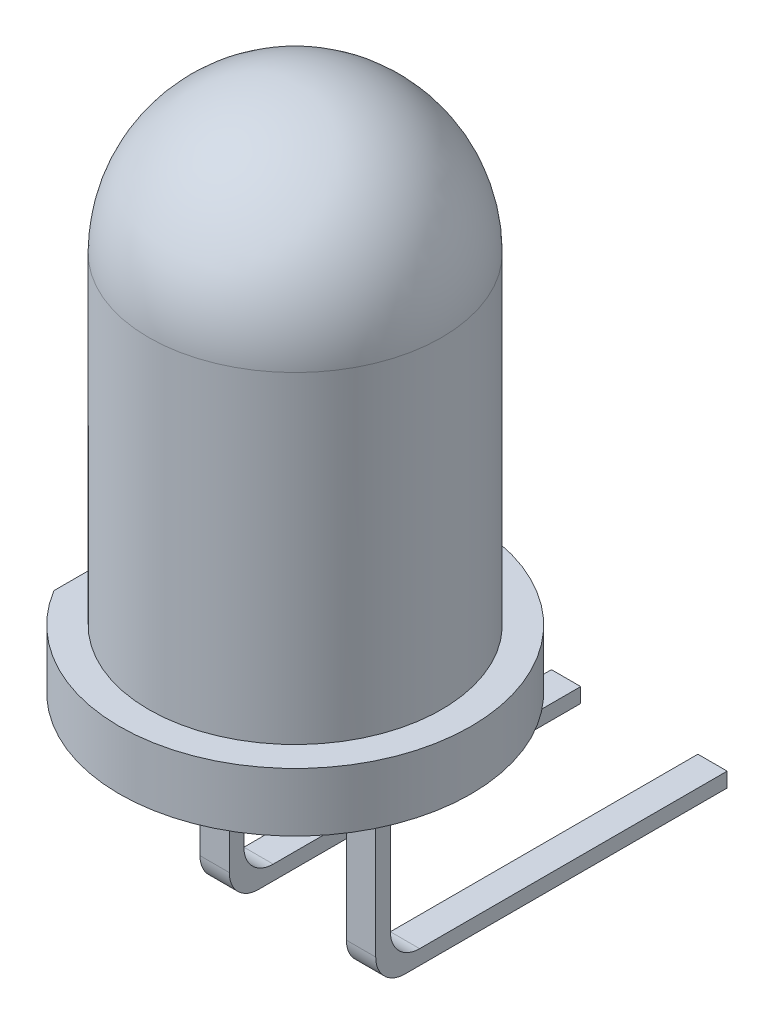
SolidWorks part; units mm, degrees
ref_plane "Front Plane" through (0, 0, 0) normal (0, 0, 1) x (1, 0, 0)
ref_plane "Top Plane" through (0, 0, 0) normal (0, 1, 0) x (1, 0, 0)
ref_plane "Right Plane" through (0, 0, 0) normal (1, 0, 0) x (0, 0, -1)
sketch "Sketch1" plane through (0, 0, 0) normal (0, 0, 1) x (1, 0, 0)
  line L0 (0, 40.4813) -> (0, -45.6712) construction
  line L3 (0, 2.5) -> (0, -5.5)
  line L5 (2.5, 0) -> (2.5, -5.5)
  line L6 (2.5, -5.5) -> (3, -5.5)
  line L7 (0, -5.5) -> (0, -6.5)
  line L8 (0, -6.5) -> (3, -6.5)
  line L9 (3, -5.5) -> (3, -6.5)
  arc A0 (2.5, 0) -> (0, 2.5) centre (0, 0) ccw
  dimension "D1" = 5
  dimension "D2" = 9
  dimension "D3" = 3
  dimension "D4" = 1
revolve "Revolve1" add sketch "Sketch1" angle 360 about L0
sketch "Sketch2" plane through (0, -6.5, 0) normal (0, -1, 0) x (1, 0, 0)
  line L0 (0, 0.7494) -> (0, -0.7682) construction
  line L1 (1, 0.125) -> (1.5, 0.125)
  line L2 (1, 0.125) -> (1, -0.125)
  line L3 (1, -0.125) -> (1.5, -0.125)
  line L4 (1.5, 0.125) -> (1.5, -0.125)
  line L5 (-1, 0.125) -> (-1, -0.125)
  line L6 (-1.5, 0.125) -> (-1.5, -0.125)
  line L7 (-1, -0.125) -> (-1.5, -0.125)
  line L8 (-1, 0.125) -> (-1.5, 0.125)
  line L9 (3.3, 0) -> (-3.3, 0) construction
  point P5 (1, 0)
  dimension "D1" = 0.25
  dimension "D2" = 0.5
  dimension "D3" = 1
extrude "Extrude1" add sketch "Sketch2" along normal blind 30
sketch "Sketch3" plane through (0, 0, 0) normal (0, 0, 1) x (1, 0, 0)
  line L0 (-1.5, -36.5) -> (-1.5, -6.5) construction
  line L1 (-1.5, -26.5) -> (-1, -26.5)
  line L2 (-1.5, -26.5) -> (-1.5, -36.5)
  line L3 (-1.5, -36.5) -> (-1, -36.5)
  line L4 (-1, -26.5) -> (-1, -36.5)
  line L5 (-1, -36.5) -> (-1, -6.5) construction
  dimension "D1" = 10
extrude "Extrude3" cut sketch "Sketch3" against normal blind 2 and the other way blind 2
sketch "Sketch4" plane through (0, -6.5, 0) normal (0, -1, 0) x (1, 0, 0)
  line L1 (-2.5675, 1.75) -> (-3.0675, 1.75)
  line L2 (-2.5675, 1.75) -> (-2.5675, -1.75)
  line L3 (-2.5675, -1.75) -> (-3.0675, -1.75)
  line L4 (-3.0675, 1.75) -> (-3.0675, -1.75)
  point P4 (-2.5675, 0)
  dimension "D1" = 3.5
  dimension "D2" = 0.5
extrude "Extrude4" cut sketch "Sketch4" against normal blind 2
sketch "Sketch5" plane through (-1.5, 0, 0) normal (-1, 0, 0) x (0, 0, 1)
  line L0 (0.125, -10.0975) -> (-5.875, -10.0975)
  line L1 (0.125, -26.5) -> (0.125, -6.5) construction
  line L2 (-5.875, -10.0975) -> (-5.875, -9.8475)
  line L3 (-5.875, -9.8475) -> (-0.125, -9.8475)
  line L4 (-0.125, -26.5) -> (-0.125, -6.5) construction
  line L5 (-0.125, -9.8475) -> (0.125, -10.0975)
  dimension "D1" = 0.25
  dimension "D2" = 6
extrude "Boss-Extrude1" add sketch "Sketch5" against normal up to surface (3 mm away) up to face at (1.5, -21.5, 0)
sketch "Sketch6" plane through (0, 0, 0.125) normal (0, 0, 1) x (1, 0, 0)
  line L0 (-1, -8.9519) -> (1, -8.9519)
  line L1 (-1, -10.0975) -> (-1, -6.5) construction
  line L2 (1, -10.0975) -> (1, -6.5) construction
  line L3 (1, -8.9519) -> (1, -10.0975)
  line L4 (1, -10.0975) -> (1.5, -10.0975)
  line L5 (1.5, -36.5) -> (1.5, -6.5) construction
  line L6 (1.5, -10.0975) -> (1.5, -37.4522)
  line L7 (1.5, -37.4522) -> (-1.5, -37.4522)
  line L8 (-1.5, -37.4522) -> (-1.5, -10.0975)
  line L9 (-1.5, -26.5) -> (-1.5, -6.5) construction
  line L10 (-1.5, -10.0975) -> (-1, -10.0975)
  line L11 (-1, -10.0975) -> (-1, -8.9519)
extrude "Cut-Extrude1" cut sketch "Sketch6" against normal blind 10
fillet "Fillet1" radius 0.5 4 edges at (1.25, -9.8475, -0.125) (-1.25, -9.8475, -0.125) (1.25, -10.0975, 0.125) (-1.25, -10.0975, 0.125)
